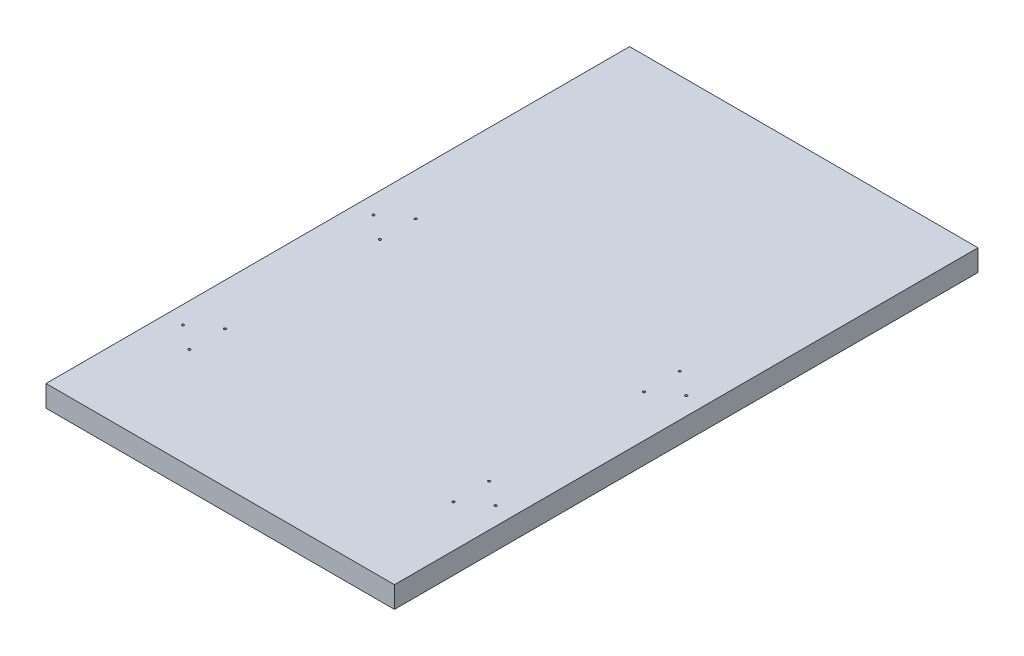
SolidWorks part; units mm, degrees
material "Дуб"
ref_plane "Спереди" through (0, 0, 0) normal (0, 0, 1) x (1, 0, 0)
ref_plane "Сверху" through (0, 0, 0) normal (0, 1, 0) x (1, 0, 0)
ref_plane "Справа" through (0, 0, 0) normal (1, 0, 0) x (0, 0, -1)
other "Configuration Table"
sketch "Эскиз1" plane through (0, 0, 0) normal (0, 1, 0) x (1, 0, 0)
  line L1 (0, 0) -> (400, 0)
  line L2 (0, 0) -> (0, 240)
  line L3 (0, 240) -> (400, 240)
  line L4 (400, 0) -> (400, 240)
  dimension "D1" = 240
  dimension "D2" = 400
extrude "Бобышка-Вытянуть1" add sketch "Эскиз1" along normal blind 18 contours L1 L4 L3 L2
sketch "Эскиз2" plane through (0, 18, 0) normal (0, 1, 0) x (1, 0, 0)
  line L0 (-44.9655, 40) -> (576.0691, 40) construction
  line L1 (0, 0) -> (400, 0) construction
  line L2 (-78.1427, 120) -> (562.0725, 120) construction
  line L3 (-44.9655, 200) -> (576.0691, 200) construction
  line L4 (250, 190.6315) -> (250, -216.1122) construction
  line L5 (350, 326.8003) -> (350, -79.9434) construction
  line L6 (400, 0) -> (400, 240) construction
  line L7 (0, 240) -> (400, 240) construction
  circle A13 centre (360.86, 55) radius 1
  circle A14 centre (360.86, 25) radius 1
  circle A15 centre (381.2858, 40) radius 1
  circle A16 centre (118.7142, 40) radius 1
  circle A17 centre (139.14, 25) radius 1
  circle A18 centre (139.14, 55) radius 1
  circle A19 centre (381.2858, 200) radius 1
  circle A20 centre (360.86, 215) radius 1
  circle A21 centre (360.86, 185) radius 1
  circle A22 centre (139.14, 185) radius 1
  circle A23 centre (139.14, 215) radius 1
  circle A24 centre (118.7142, 200) radius 1
  dimension "D3" = 50
  dimension "D5" = 25.3419
  dimension "D7" = 10.86
  dimension "D1" = 40
  dimension "D2" = 160
  dimension "D4" = 30
  dimension "D6" = 25.3419
  dimension "D8" = 100
  dimension "D9" = 120
  dimension "D10" = 120
  dimension "D11" = 240
extrude "Вырез-Вытянуть1" cut sketch "Эскиз2" against normal through all
sketch "Эскиз3" plane through (0, 18, 0) normal (0, 1, 0) x (1, 0, 0)
  line L0 (400, 0) -> (400, 240) construction
  line L2 (103.7142, 230) -> (396.2858, 230)
  line L3 (103.7142, 230) -> (103.7142, 10)
  line L4 (103.7142, 10) -> (396.2858, 10)
  line L5 (396.2858, 230) -> (396.2858, 10)
  line L7 (504.6059, -42.839) -> (-111.3728, -42.839)
  line L8 (504.6059, -42.839) -> (504.6059, 284.7195)
  line L9 (504.6059, 284.7195) -> (-111.3728, 284.7195)
  line L10 (-111.3728, -42.839) -> (-111.3728, 284.7195)
  circle A0 centre (381.2858, 200) radius 1 construction
  circle A1 centre (360.86, 215) radius 1 construction
  circle A2 centre (118.7142, 200) radius 1 construction
  circle A3 centre (381.2858, 40) radius 1 construction
  circle A4 centre (360.86, 25) radius 1 construction
  circle A5 centre (139.14, 215) radius 1 construction
  dimension "D3" = 15
  dimension "D5" = 15
  dimension "D6" = 15
  dimension "D1" = 18.7142
  dimension "D2" = 39.14
  dimension "D4" = 15
extrude "Вырез-Вытянуть2" cut sketch "Эскиз3" against normal through all
sketch "Эскиз4" plane through (0, 0, -230) normal (0, 0, -1) x (-1, 0, 0)
  line L1 (-396.2858, 18) -> (-103.7142, 18)
  line L2 (-396.2858, 18) -> (-396.2858, 0)
  line L3 (-396.2858, 0) -> (-103.7142, 0)
  line L4 (-103.7142, 18) -> (-103.7142, 0)
extrude "Бобышка-Вытянуть2" add sketch "Эскиз4" along normal blind 200
sketch "Эскиз5" plane through (0, 0, -10) normal (0, 0, 1) x (1, 0, 0)
  line L0 (103.7142, 0) -> (396.2858, 0) construction
  line L1 (103.7142, 0) -> (396.2858, 0)
  line L2 (103.7142, 0) -> (103.7142, 18)
  line L3 (103.7142, 18) -> (396.2858, 18)
  line L4 (396.2858, 0) -> (396.2858, 18)
extrude "Бобышка-Вытянуть3" add sketch "Эскиз5" along normal blind 70
